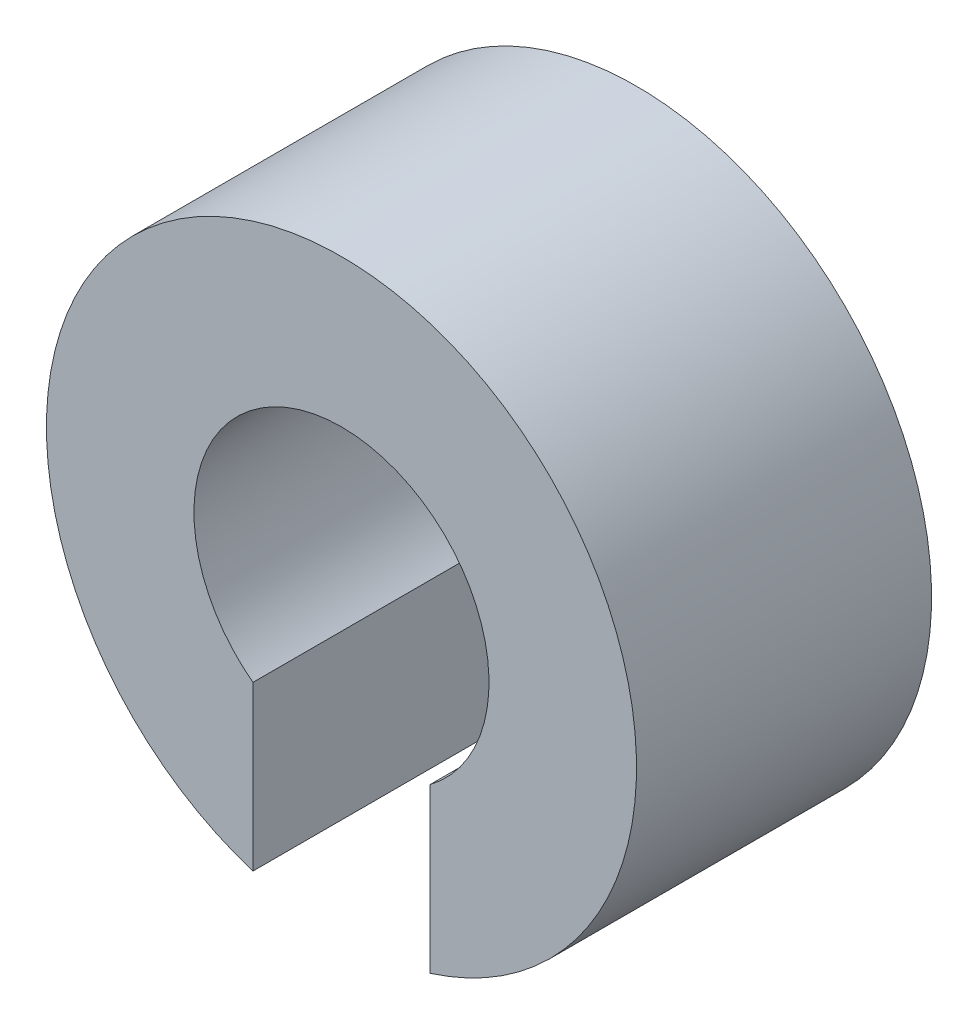
SolidWorks part; units mm, degrees
ref_plane "正面" through (0, 0, 0) normal (0, 0, 1) x (1, 0, 0)
ref_plane "平面" through (0, 0, 0) normal (0, 1, 0) x (1, 0, 0)
ref_plane "右側面" through (0, 0, 0) normal (1, 0, 0) x (0, 0, -1)
sketch "ｽｹｯﾁ1" plane through (0, 0, 0) normal (0, 0, 1) x (1, 0, 0)
  line L2 (-1.5, -4.7697) -> (-1.5, -2)
  line L4 (1.5, -4.7697) -> (1.5, -2)
  line L5 (-1.5, -8.2982) -> (1.5, -1.7018) construction
  line L6 (-1.5, -1.7018) -> (1.5, -8.2982) construction
  arc A0 (1.5, -2) -> (-1.5, -2) centre (0, 0) ccw
  arc A1 (1.5, -4.7697) -> (-1.5, -4.7697) centre (0, 0) ccw
  point P4 (0, -5)
  dimension "D1" = 5
  dimension "D2" = 10
  dimension "D3" = 3
extrude "ﾎﾞｽ - 押し出し1" add sketch "ｽｹｯﾁ1" along normal blind 5
